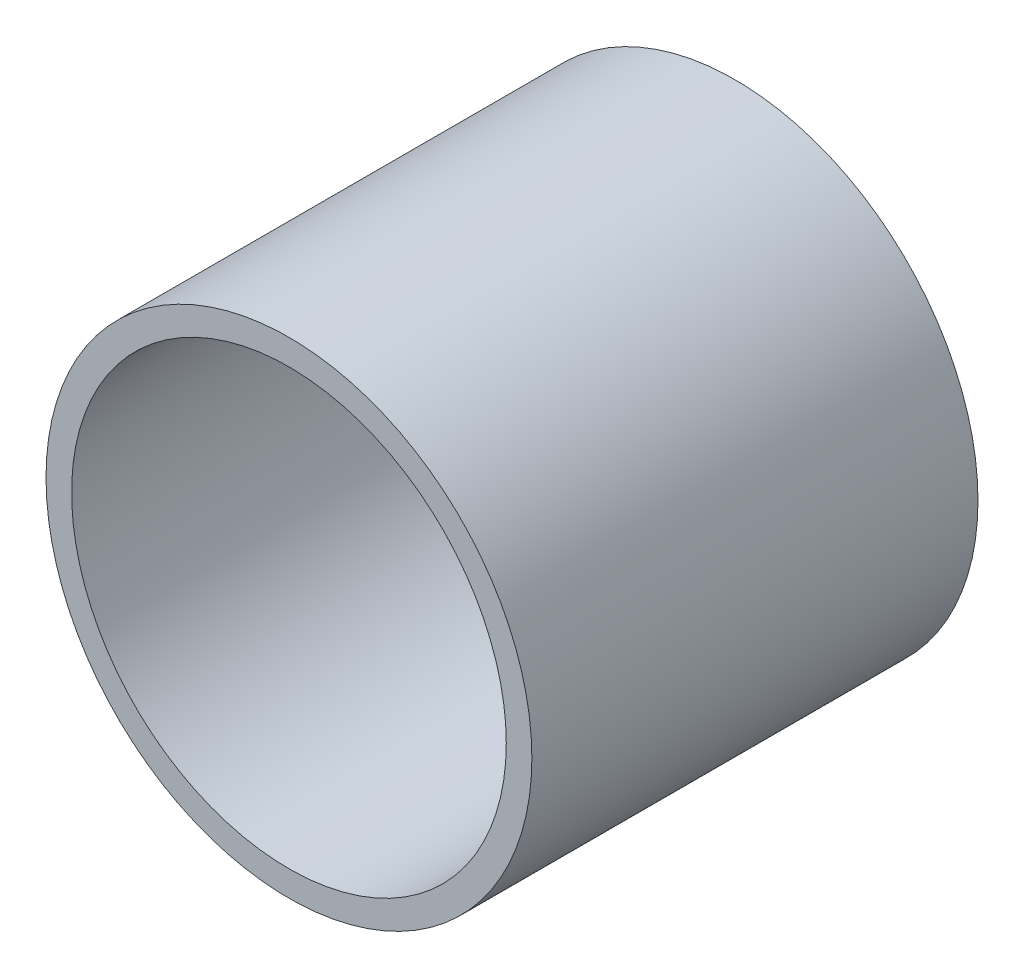
SolidWorks part; units mm, degrees
material "PVC Rigid"
ref_plane "Front Plane" through (0, 0, 0) normal (0, 0, 1) x (1, 0, 0)
ref_plane "Top Plane" through (0, 0, 0) normal (0, 1, 0) x (1, 0, 0)
ref_plane "Right Plane" through (0, 0, 0) normal (1, 0, 0) x (0, 0, -1)
sketch "Sketch1" plane through (0, 0, 0) normal (0, 0, 1) x (1, 0, 0)
  circle A0 centre (0, 0) radius 57.15
  dimension "Pipe OD" = 114.3
extrude "Extrude-Thin1" add sketch "Sketch1" along normal mid plane 104.95 thin thin type one direction reverse wall 6.0198
